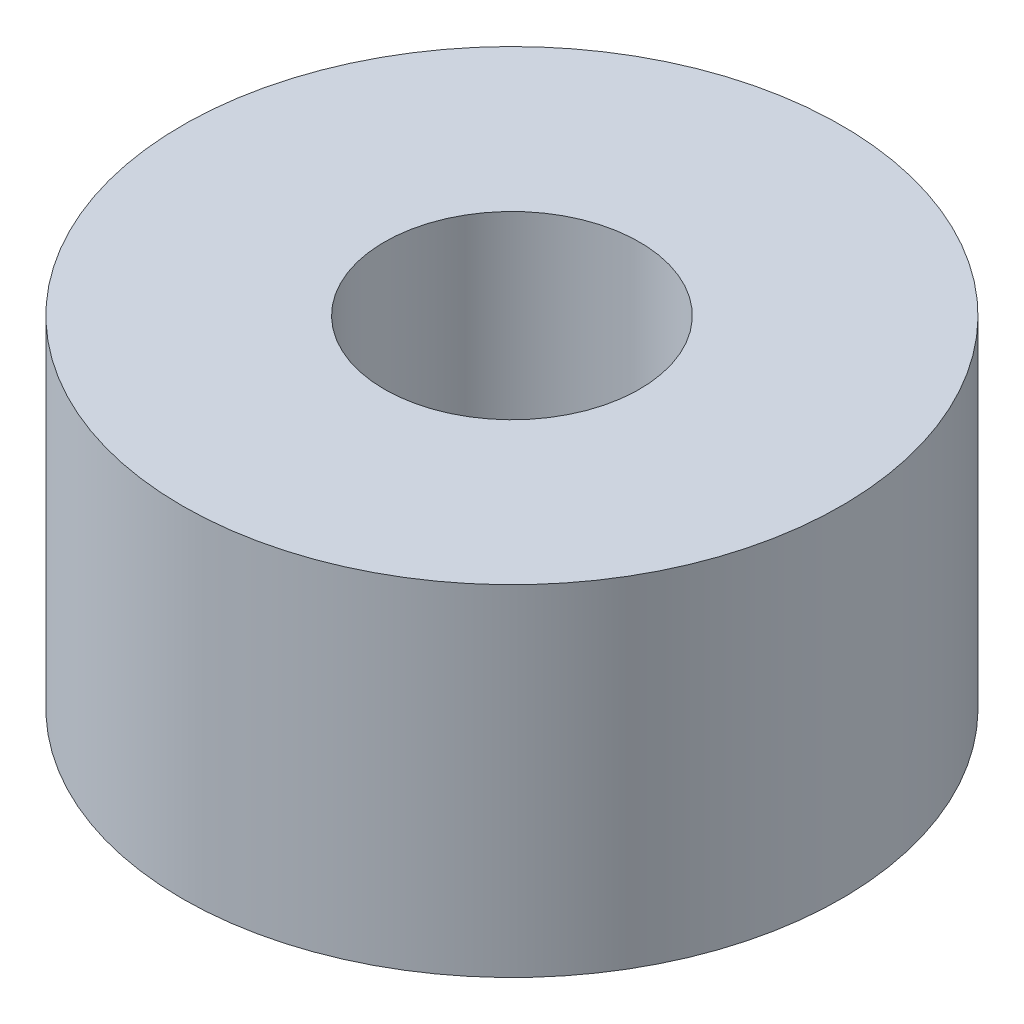
SolidWorks part; units mm, degrees
ref_plane "Front Plane" through (0, 0, 0) normal (0, 0, 1) x (1, 0, 0)
ref_plane "Top Plane" through (0, 0, 0) normal (0, 1, 0) x (1, 0, 0)
ref_plane "Right Plane" through (0, 0, 0) normal (1, 0, 0) x (0, 0, -1)
other "Bounding Box"
ref_plane "Default Plane" through (13.8565, 3.175, 6.7999) normal (0, -1, 0) x (-1, 0, 0)
sketch "Sketch1" plane through (0, 0, 0) normal (0, 1, 0) x (1, 0, 0)
  circle A0 centre (0, 0) radius 1.524
  circle A1 centre (0, 0) radius 3.937
  dimension "D1" = 3.048
  dimension "D2" = 7.874
extrude "Boss-Extrude1" add sketch "Sketch1" along normal blind 4.064
